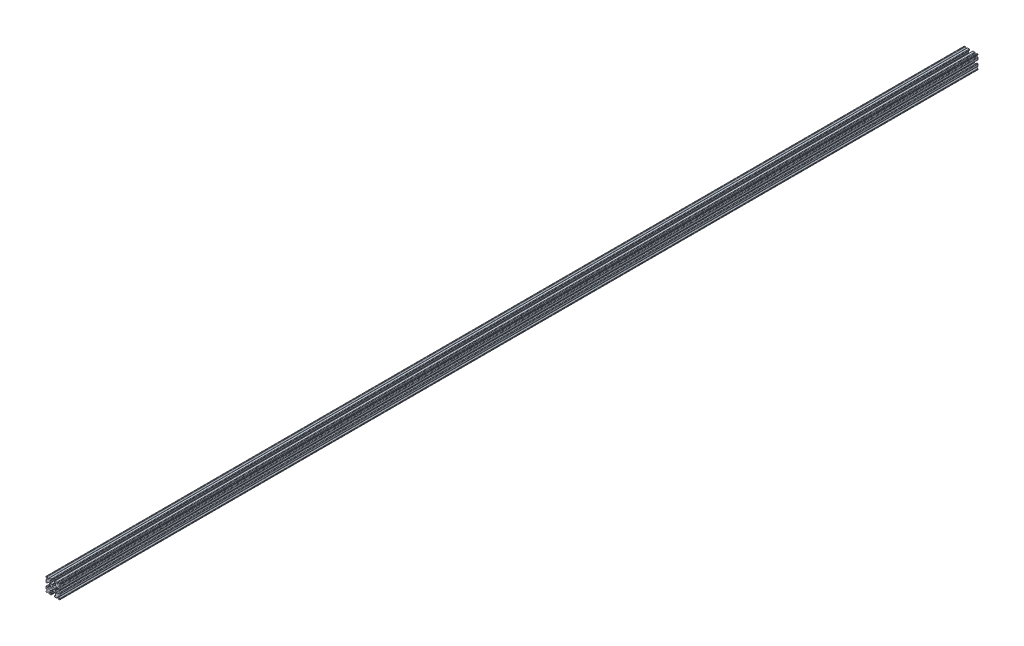
SolidWorks part; units mm, degrees
ref_plane "Front Plane" through (0, 0, 0) normal (0, 0, 1) x (1, 0, 0)
ref_plane "Top Plane" through (0, 0, 0) normal (0, 1, 0) x (1, 0, 0)
ref_plane "Right Plane" through (0, 0, 0) normal (1, 0, 0) x (0, 0, -1)
sketch "Sketch1" plane through (0, 0, 0) normal (0, 0, 1) x (1, 0, 0)
  line L1 (-7.5, -7.5) -> (7.5, -7.5)
  line L2 (-7.5, -7.5) -> (-7.5, 7.5)
  line L3 (-7.5, 7.5) -> (7.5, 7.5)
  line L4 (7.5, -7.5) -> (7.5, 7.5)
  line L5 (-7.5, -7.5) -> (7.5, 7.5) construction
  line L6 (-7.5, 7.5) -> (7.5, -7.5) construction
  circle A0 centre (0, 0) radius 1.25
  point P0 (0, 0)
  dimension "D2" = 2.5
  dimension "D1" = 15
extrude "Boss-Extrude1" add sketch "Sketch1" along normal mid plane 1000
fillet "Fillet1" radius 0.25 4 edges at (7.5, -7.5, 0) (-7.5, -7.5, 0) (7.5, 7.5, 0) (-7.5, 7.5, 0)
sketch "Sketch2" plane through (0, 0, 500) normal (0, 0, 1) x (1, 0, 0)
  line L0 (-7.5, 7.25) -> (-7.5, -7.25) construction
  line L1 (-7.5, 1.6) -> (-6.1, 1.6)
  line L2 (-7.5, 1.6) -> (-7.5, -1.6)
  line L3 (-7.5, -1.6) -> (-6.1, -1.6)
  line L4 (-6.1, 1.6) -> (-6.1, 2.9)
  line L5 (0, 0) -> (-12.1036, 0) construction
  line L6 (-6.1, -2.9) -> (-3.4, -2.9)
  line L7 (0, 0) -> (-7.25, 7.25) construction
  line L8 (-6.1, 2.9) -> (-3.4, 2.9)
  line L9 (-3.4, -2.9) -> (-3.4, 2.9)
  line L10 (55, 0) -> (-55, 0) construction
  line L11 (-6.1, -2.9) -> (-6.1, -1.6)
  line L12 (2.9, 6.1) -> (1.6, 6.1)
  line L13 (2.9, 3.4) -> (-2.9, 3.4)
  line L14 (-2.9, 6.1) -> (-2.9, 3.4)
  line L15 (2.9, 6.1) -> (2.9, 3.4)
  line L16 (-1.6, 6.1) -> (-2.9, 6.1)
  line L17 (1.6, 7.5) -> (1.6, 6.1)
  line L18 (-1.6, 7.5) -> (1.6, 7.5)
  line L19 (-1.6, 7.5) -> (-1.6, 6.1)
  line L20 (-1.6, -7.5) -> (-1.6, -6.1)
  line L21 (-1.6, -7.5) -> (1.6, -7.5)
  line L22 (1.6, -7.5) -> (1.6, -6.1)
  line L23 (-1.6, -6.1) -> (-2.9, -6.1)
  line L24 (2.9, -6.1) -> (2.9, -3.4)
  line L25 (-2.9, -6.1) -> (-2.9, -3.4)
  line L26 (2.9, -3.4) -> (-2.9, -3.4)
  line L27 (2.9, -6.1) -> (1.6, -6.1)
  line L28 (6.1, -2.9) -> (6.1, -1.6)
  line L29 (3.4, -2.9) -> (3.4, 2.9)
  line L30 (6.1, 2.9) -> (3.4, 2.9)
  line L31 (6.1, -2.9) -> (3.4, -2.9)
  line L32 (6.1, 1.6) -> (6.1, 2.9)
  line L33 (7.5, -1.6) -> (6.1, -1.6)
  line L34 (7.5, 1.6) -> (7.5, -1.6)
  line L35 (7.5, 1.6) -> (6.1, 1.6)
  dimension "D1" = 3.2
  dimension "D2" = 5.8
  dimension "D3" = 1.4
  dimension "D4" = 2.7
extrude "Cut-Extrude1" cut sketch "Sketch2" against normal through all
sketch "Sketch4" plane through (0, 0, 500) normal (0, 0, 1) x (1, 0, 0)
  line L0 (-3.4, 2.9) -> (-2.75, 0)
  line L1 (55, 0) -> (-55, 0) construction
  line L2 (-2.75, 0) -> (-3.4, -2.9)
  line L3 (-3.4, -2.9) -> (-3.4, 2.9) construction
  line L4 (-3.4, 2.9) -> (-3.4, -2.9)
  line L5 (-2.9, 3.4) -> (0, 2.75)
  line L6 (0, 2.75) -> (2.9, 3.4)
  line L7 (2.9, 3.4) -> (-2.9, 3.4)
  line L8 (3.4, 2.9) -> (2.75, 0)
  line L9 (2.75, 0) -> (3.4, -2.9)
  line L10 (3.4, -2.9) -> (3.4, 2.9)
  line L11 (-2.9, -3.4) -> (0, -2.75)
  line L12 (0, -2.75) -> (2.9, -3.4)
  line L13 (2.9, -3.4) -> (-2.9, -3.4)
  circle A2 centre (0, 0) radius 2.75
  circle A3 centre (0, 0) radius 2.75 construction
  dimension "D1" = 1.5
extrude "Cut-Extrude3" cut sketch "Sketch4" against normal through all
fillet "Fillet3" radius 0.5 16 edges at (-6.1, -1.6, 0) (-7.5, -1.6, 0) (-6.1, 1.6, 0) (-7.5, 1.6, 0) (-1.6, -7.5, 0) (-1.6, -6.1, 0) (1.6, -7.5, 0) (1.6, -6.1, 0) (6.1, -1.6, 0) (7.5, -1.6, 0) (7.5, 1.6, 0) (6.1, 1.6, 0) (1.6, 7.5, 0) (1.6, 6.1, 0) (-1.6, 7.5, 0) (-1.6, 6.1, 0)
fillet "Fillet4" radius 0.5 8 edges at (-3.4, 2.9, 0) (-3.4, -2.9, 0) (2.9, -3.4, 0) (-2.9, -3.4, 0) (3.4, -2.9, 0) (3.4, 2.9, 0) (-2.9, 3.4, 0) (2.9, 3.4, 0)
fillet "Fillet5" radius 3 4 edges at (0, -2.75, 0) (2.75, 0, 0) (-2.75, 0, 0) (0, 2.75, 0)
fillet "Fillet6" radius 0.2 8 edges at (-2.9, -6.1, 0) (2.9, -6.1, 0) (6.1, -2.9, 0) (6.1, 2.9, 0) (2.9, 6.1, 0) (-2.9, 6.1, 0) (-6.1, -2.9, 0) (-6.1, 2.9, 0)
sketch "Sketch5" plane through (0, 0, 500) normal (0, 0, 1) x (1, 0, 0)
  line L0 (0, 0) -> (-7.25, 7.25) construction
  line L1 (-7.5, 6.4393) -> (-5.4607, 4.4)
  line L2 (-6.4393, 7.5) -> (-4.4, 5.4607)
  line L3 (-7.5, 4.4) -> (-5.4607, 4.4)
  line L4 (-3.8003, 2.9) -> (-5.9, 2.9) construction
  line L5 (0, 0) -> (-12.1819, 0) construction
  line L6 (-4.4, 7.5) -> (-4.4, 5.4607)
  line L7 (-2.9, 5.9) -> (-2.9, 3.8003) construction
  line L8 (-7.5, 6.4393) -> (-7.5, 4.4)
  line L9 (-7.5, 7.25) -> (-7.5, 2.1) construction
  line L10 (2.1, -7.5) -> (7.25, -7.5) construction
  line L11 (7.5, -7.25) -> (7.5, -2.1) construction
  line L12 (7.25, 7.5) -> (2.1, 7.5) construction
  line L13 (-2.1, 7.5) -> (-7.25, 7.5) construction
  line L14 (-4.4, 7.5) -> (-6.4393, 7.5)
  line L16 (55, 0) -> (-55, 0) construction
  line L17 (0, 0) -> (0, 10.993) construction
  line L18 (0, -54.6431) -> (0, 54.6431) construction
  line L20 (4.4, 7.5) -> (6.4393, 7.5)
  line L22 (7.5, 6.4393) -> (7.5, 4.4)
  line L23 (4.4, 7.5) -> (4.4, 5.4607)
  line L24 (7.5, 4.4) -> (5.4607, 4.4)
  line L25 (6.4393, 7.5) -> (4.4, 5.4607)
  line L26 (7.5, 6.4393) -> (5.4607, 4.4)
  line L27 (7.5, -6.4393) -> (5.4607, -4.4)
  line L28 (6.4393, -7.5) -> (4.4, -5.4607)
  line L29 (7.5, -4.4) -> (5.4607, -4.4)
  line L30 (4.4, -7.5) -> (4.4, -5.4607)
  line L31 (7.5, -6.4393) -> (7.5, -4.4)
  line L33 (4.4, -7.5) -> (6.4393, -7.5)
  line L36 (-4.4, -7.5) -> (-6.4393, -7.5)
  line L38 (-7.5, -6.4393) -> (-7.5, -4.4)
  line L39 (-4.4, -7.5) -> (-4.4, -5.4607)
  line L40 (-7.5, -4.4) -> (-5.4607, -4.4)
  line L41 (-6.4393, -7.5) -> (-4.4, -5.4607)
  line L42 (-7.5, -6.4393) -> (-5.4607, -4.4)
  dimension "D1" = 1.5
  dimension "D2" = 1.5
  dimension "D3" = 1.5
extrude "Cut-Extrude4" cut sketch "Sketch5" against normal through all
fillet "Fillet8" radius 0.5 24 edges at (-5.4607, 4.4, 0) (-7.5, 4.4, 0) (-5.4607, -4.4, 0) (-7.5, -4.4, 0) (-4.4, -7.5, 0) (-4.4, -5.4607, 0) (4.4, -7.5, 0) (4.4, -5.4607, 0) (5.4607, -4.4, 0) (7.5, -4.4, 0) (7.5, 4.4, 0) (5.4607, 4.4, 0) (4.4, 5.4607, 0) (4.4, 7.5, 0) (-4.4, 5.4607, 0) (-4.4, 7.5, 0) (-6.4393, 7.5, 0) (-7.5, 6.4393, 0) (6.4393, 7.5, 0) (7.5, 6.4393, 0) (6.4393, -7.5, 0) (7.5, -6.4393, 0) (-6.4393, -7.5, 0) (-7.5, -6.4393, 0)
sketch "Sketch6" plane through (0, 0, 500) normal (0, 0, 1) x (1, 0, 0)
  line L0 (0, 0) -> (0, 11.013) construction
  line L1 (0.6561, 2.8971) -> (2.1235, 2.8971) construction
  line L2 (0, -54.6431) -> (0, 54.6431) construction
  line L3 (0, 0) -> (7.25, 7.25) construction
  line L4 (7.5, 0.8255) -> (7.5, -0.8255)
  line L5 (2.3471, 0.8255) -> (7.5, 0.8255)
  line L6 (0, 0) -> (12.4016, 0) construction
  line L7 (0.8255, -7.5) -> (-0.8255, -7.5)
  line L8 (2.3471, -0.8255) -> (2.3471, 0.8255)
  line L9 (0.8255, -2.3471) -> (0.8255, -7.5)
  line L10 (7.5, -0.8255) -> (2.3471, -0.8255)
  line L11 (-7.5, -0.8255) -> (-2.3471, -0.8255)
  line L12 (-2.3471, -0.8255) -> (-2.3471, 0.8255)
  line L13 (-0.8255, -2.3471) -> (0.8255, -2.3471)
  line L14 (-0.8255, 7.5) -> (-0.8255, 2.3471)
  line L15 (-0.8255, 2.3471) -> (0.8255, 2.3471)
  line L16 (-0.8255, -7.5) -> (-0.8255, -2.3471)
  line L17 (0.8255, 2.3471) -> (0.8255, 7.5)
  line L18 (0.8255, 7.5) -> (-0.8255, 7.5)
  line L19 (3.9, 7.5) -> (2.1, 7.5) construction
  line L20 (-2.3471, 0.8255) -> (-7.5, 0.8255)
  line L21 (-7.5, 0.8255) -> (-7.5, -0.8255)
  point P5 (0, -2.5973)
  point P7 (0, 2.5973)
  dimension "D3" = 0.55
  dimension "D1" = 1.651
extrude "Cut-Extrude5" cut sketch "Sketch6" against normal through all
fillet "Fillet10" radius 0.2 16 edges at (-2.935, 0.8255, 0) (-2.935, -0.8255, 0) (2.935, -0.8255, 0) (2.935, 0.8255, 0) (0.8255, 2.935, 0) (-0.8255, 2.935, 0) (-2.3471, 0.8255, 0) (-2.3471, -0.8255, 0) (0.8255, 2.3471, 0) (-0.8255, 2.3471, 0) (2.3471, 0.8255, 0) (2.3471, -0.8255, 0) (0.8255, -2.935, 0) (0.8255, -2.3471, 0) (-0.8255, -2.3471, 0) (-0.8255, -2.935, 0)
